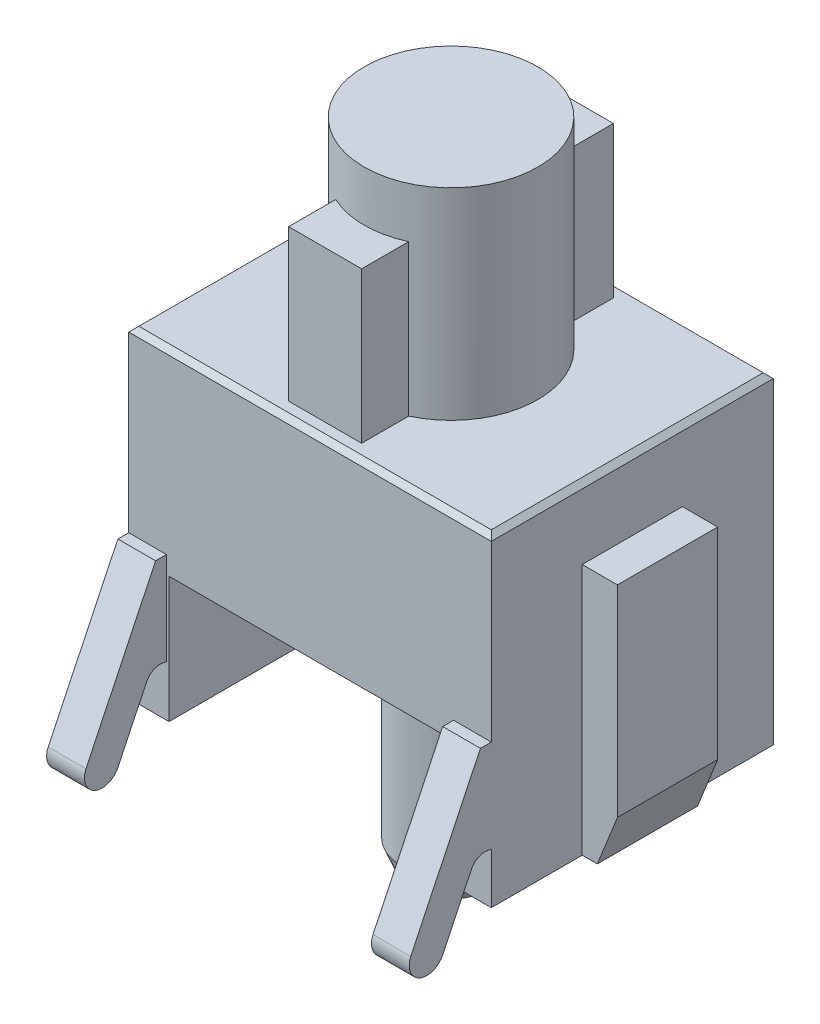
SolidWorks part; units mm, degrees
ref_plane "Front Plane" through (0, 0, 0) normal (0, 0, 1) x (1, 0, 0)
ref_plane "Top Plane" through (0, 0, 0) normal (0, 1, 0) x (1, 0, 0)
ref_plane "Right Plane" through (0, 0, 0) normal (1, 0, 0) x (0, 0, -1)
sketch "Sketch1" plane through (0, 0, 0) normal (0, 1, 0) x (1, 0, 0)
  line L1 (-3.6, -2.8) -> (3.6, -2.8)
  line L2 (-3.6, -2.8) -> (-3.6, 2.8)
  line L3 (-3.6, 2.8) -> (3.6, 2.8)
  line L4 (3.6, -2.8) -> (3.6, 2.8)
  line L5 (-3.6, -2.8) -> (3.6, 2.8) construction
  line L6 (-3.6, 2.8) -> (3.6, -2.8) construction
  point P0 (0, 0)
  dimension "D1" = 7.2
  dimension "D2" = 5.6
extrude "Body" add sketch "Sketch1" along normal blind 6.4
chamfer "Body Chamfer" distance 0.1 angle 45 4 edges at (0, 6.4, 2.8) (3.6, 6.4, 0) (0, 6.4, -2.8) (-3.6, 6.4, 0)
sketch "Sketch2" plane through (0, 6.4, 0) normal (0, 1, 0) x (1, 0, 0)
  circle A0 centre (0, 0) radius 1.725
  dimension "D1" = 3.45
extrude "Mount" add sketch "Sketch2" along normal blind 4
sketch "Sketch3" plane through (0, 6.4, 0) normal (0, 1, 0) x (1, 0, 0)
  line L1 (-0.725, -2.5) -> (0.725, -2.5)
  line L2 (-0.725, -2.5) -> (-0.725, 2.5)
  line L3 (-0.725, 2.5) -> (0.725, 2.5)
  line L4 (0.725, -2.5) -> (0.725, 2.5)
  line L5 (-0.725, -2.5) -> (0.725, 2.5) construction
  line L6 (-0.725, 2.5) -> (0.725, -2.5) construction
  point P0 (0, 0)
  dimension "D1" = 5
  dimension "D2" = 1.45
extrude "Mount Rails" add sketch "Sketch3" along normal blind 3
sketch "Sketch4" plane through (0, 0, 0) normal (0, -1, 0) x (1, 0, 0)
  circle A0 centre (0, 0) radius 2.25
  dimension "D1" = 4.5
extrude "Body Cut 1" cut sketch "Sketch4" against normal blind 4.8
sketch "Sketch5" plane through (0, 0, 0) normal (0, -1, 0) x (1, 0, 0)
  line L0 (-3.6, 2.8) -> (3.6, 2.8) construction
  line L1 (-2.8, -2.8) -> (2.8, -2.8)
  line L2 (-2.8, -2.8) -> (-2.8, 2.8)
  line L3 (-2.8, 2.8) -> (2.8, 2.8)
  line L4 (2.8, -2.8) -> (2.8, 2.8)
  line L5 (-2.8, -2.8) -> (2.8, 2.8) construction
  line L6 (-2.8, 2.8) -> (2.8, -2.8) construction
  point P0 (0, 0)
  dimension "D1" = 5.6
extrude "Body Cut 2" cut sketch "Sketch5" against normal blind 2.5
sketch "Sketch6" plane through (0, 4.8, 0) normal (0, -1, 0) x (1, 0, 0)
  circle A0 centre (0, 0) radius 0.975
  dimension "D1" = 1.95
extrude "Pole" add sketch "Sketch6" along normal blind 7.3
chamfer "Pole Chamfer" distance 0.5 distance2 0.2 1 edges at (0, -2.5, -0.975)
sketch "Sketch7" plane through (3.6, 0, 0) normal (1, 0, 0) x (0, 0, -1)
  line L1 (-0.995, 5) -> (0.995, 5)
  line L2 (-0.995, 5) -> (-0.995, 0)
  line L3 (-0.995, 0) -> (0.995, 0)
  line L4 (0.995, 5) -> (0.995, 0)
  line L5 (-0.995, 5) -> (0.995, 0) construction
  line L6 (-0.995, 0) -> (0.995, 5) construction
  line L7 (-2.8, 0) -> (2.8, 0) construction
  point P0 (0, 2.5)
  dimension "D1" = 1.99
  dimension "D3" = 5
extrude "Right Rail" add sketch "Sketch7" along normal blind 0.7
mirror "Rail Mirror" about plane through (0, 0, 0) normal (1, 0, 0) of "Right Rail"
chamfer "Right Rail Chamfer" distance 0.4 distance2 1 1 edges at (4.3, 0, 0)
chamfer "Left Rail Chamfer" distance 1 distance2 0.4 1 edges at (-4.3, 0, 0)
sketch "Sketch8" plane through (3.6, 0, 0) normal (1, 0, 0) x (0, 0, -1)
  line L0 (-3.0162, 2.8492) -> (-4.4, -0.0362)
  line L5 (-3.0162, 2.8492) -> (-2.8, 2.8492)
  line L7 (-3.76, -0.3196) -> (-3.1978, 0.8525)
  line L8 (-2.8, 1) -> (-2.8, 2.8492)
  line L9 (-2.8, 0) -> (-0.995, 0) construction
  line L10 (-2.8, 6.3) -> (-2.8, 0) construction
  line L12 (-4.4, -0.0362) -> (-4.08, -0.1779) construction
  line L13 (-4.08, -0.1779) -> (-3.76, -0.3196) construction
  line L14 (-3.1978, 0.8525) -> (-2.9252, 0.7274) construction
  line L15 (-2.9252, 0.7274) -> (-2.8, 1) construction
  arc A0 (-3.1978, 0.8525) -> (-2.8, 1) centre (-2.9252, 0.7274) cw
  arc A1 (-4.4, -0.0362) -> (-3.76, -0.3196) centre (-4.08, -0.1779) ccw
  dimension "D6" = 0.35
  dimension "D7" = 0.3
  dimension "D1" = 1
  dimension "D2" = 1.6
  dimension "D3" = 3.2
  dimension "D4" = 1.3
extrude "Right Leg" add sketch "Sketch8" against normal blind 0.75
mirror "Leg Mirror" about plane through (0, 0, 0) normal (1, 0, 0) of "Right Leg"
